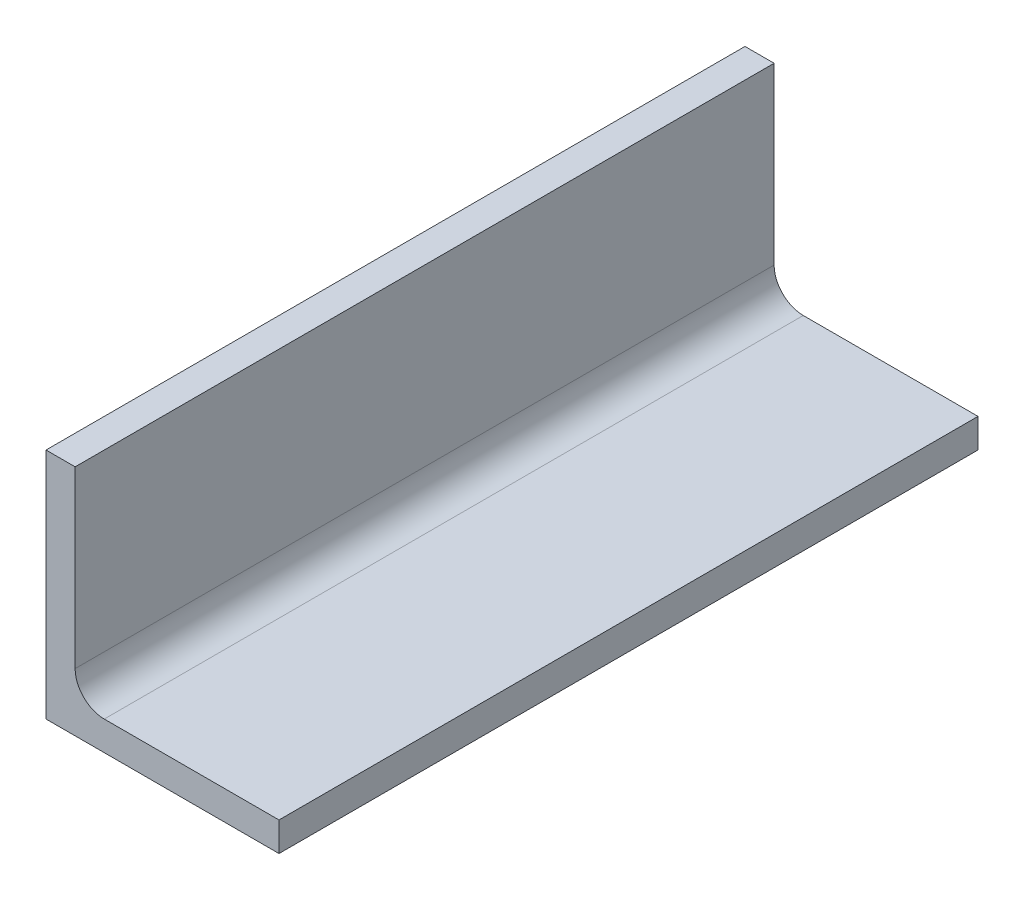
SolidWorks part; units mm, degrees
ref_plane "Front Plane" through (0, 0, 0) normal (0, 0, 1) x (1, 0, 0)
ref_plane "Top Plane" through (0, 0, 0) normal (0, 1, 0) x (1, 0, 0)
ref_plane "Right Plane" through (0, 0, 0) normal (1, 0, 0) x (0, 0, -1)
sketch "Sketch2" plane through (0, 0, 0) normal (0, 0, 1) x (1, 0, 0)
  line L0 (0, 0) -> (0, 50.8)
  line L1 (0, 50.8) -> (6.35, 50.8)
  line L2 (6.35, 50.8) -> (6.35, 12.7)
  line L3 (12.7, 6.35) -> (50.8, 6.35)
  line L4 (50.8, 6.35) -> (50.8, 0)
  line L5 (50.8, 0) -> (0, 0)
  arc A0 (12.7, 6.35) -> (6.35, 12.7) centre (12.7, 12.7) cw
  dimension "D4" = 6.35
  dimension "D1" = 6.35
  dimension "D2" = 50.8
  dimension "D3" = 50.8
extrude "Boss-Extrude1" add sketch "Sketch2" along normal mid plane 152.4
